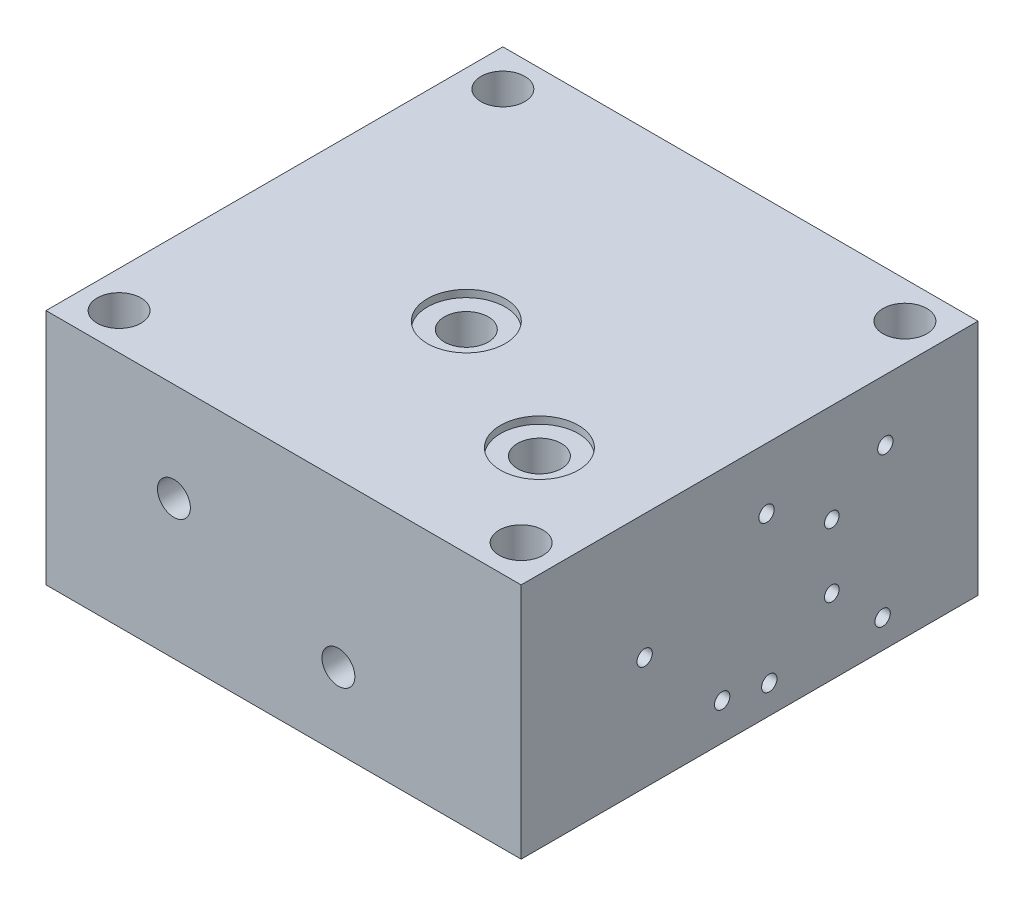
SolidWorks part; units mm, degrees
ref_plane "前视基准面" through (0, 0, 0) normal (0, 0, 1) x (1, 0, 0)
ref_plane "上视基准面" through (0, 0, 0) normal (0, 1, 0) x (1, 0, 0)
ref_plane "右视基准面" through (0, 0, 0) normal (1, 0, 0) x (0, 0, -1)
sketch "草图2" plane through (0, 0, 0) normal (0, 1, 0) x (1, 0, 0)
  line L1 (-65, -62.5) -> (65, -62.5)
  line L2 (-65, -62.5) -> (-65, 62.5)
  line L3 (-65, 62.5) -> (65, 62.5)
  line L4 (65, -62.5) -> (65, 62.5)
  line L5 (-65, -62.5) -> (65, 62.5) construction
  line L6 (-65, 62.5) -> (65, -62.5) construction
  circle A0 centre (-55, 52.5) radius 6
  circle A1 centre (55, 52.5) radius 6
  circle A2 centre (55, -52.5) radius 6
  circle A3 centre (-55, -52.5) radius 6
  point P0 (0, 0)
  dimension "D1" = 10
  dimension "D2" = 10
  dimension "D3" = 2
  dimension "D4" = 2
extrude "凸台-拉伸1" add sketch "草图2" along normal blind 65 contours A2 | A3 | A1 | L2 L3 L4 L1 | A0
sketch "草图19" plane through (-65, 0, 0) normal (-1, 0, 0) x (0, 0, 1)
  line L0 (-62.5, 65) -> (-62.5, 38)
  line L1 (-62.5, 65) -> (-62.5, 0) construction
  line L2 (-62.5, 38) -> (-22.5, 38)
hole_wizard "Ø4.0 (4) 直径孔5" positions "3D草图6" profile "草图20" hole size "Ø4.0" standard "GB" end condition through all
sketch3d "3D草图6"
  point P0 (-65, 38, -22.5)
sketch "草图20" plane through (-65, 38, -22.5) normal (0, 1, 0) x (0, 0, 1)
  line L0 (0, 0) -> (0, 130)
  line L1 (0, 130) -> (2, 130)
  line L2 (2, 130) -> (2, 0)
  line L5 (2, 0) -> (0, 0)
  line L11 (0, -6.35) -> (0, 107.95) construction
  dimension "通孔孔直径" = 4
  dimension "通孔孔深度" = 130
sketch "草图21" plane through (0, 0, -62.5) normal (0, 0, -1) x (-1, 0, 0)
  point P10 (-4.7, 9.8)
  point P11 (-12.2, 20.5)
  point P12 (-30.5, 9.8)
  point P13 (-23, 20.5)
  point P22 (-30.5, 31.2)
  point P23 (-4.7, 31.2)
  point P24 (-32.5, 20.5)
  point P25 (-17.6, 30.4)
  dimension "D3" = 27.8
  dimension "D4" = 12.9
  dimension "D5" = 10.7
  dimension "D6" = 20.6
  dimension "D7" = 21.4
  dimension "D8" = 25.8
  dimension "D1" = 7.5
  dimension "D2" = 18.3
sketch "草图26" plane through (65, 0, 0) normal (1, 0, 0) x (0, 0, -1)
  point P2 (-28.7046, 20.5)
  point P8 (5.4, 7.8)
  point P9 (4.65, 48.3)
  point P10 (37.15, 48.3)
  point P11 (36.4, 7.8)
  point P12 (22.4954, 38)
  point P13 (22.4954, 20.5)
  dimension "D1" = 40.5
  dimension "D2" = 0.75
  dimension "D3" = 31
  dimension "D4" = 31.75
  dimension "D5" = 30.2
  dimension "D6" = 12.7
hole_wizard "M5 螺纹孔3" positions "3D草图11" profile "草图27" tap size "M5" standard "GB"
sketch3d "3D草图11"
  point P0 (65, 48.3, -4.65)
  point P3 (65, 48.3, -37.15)
  point P6 (65, 7.8, -36.4)
  point P9 (65, 7.8, -5.4)
sketch "草图27" plane through (65, 48.3, -4.65) normal (0, 1, 0) x (0, 0, -1)
  line L0 (0, 0) -> (0, 13.2618)
  line L1 (0, 13.2618) -> (2.1, 12)
  line L2 (2.1, 12) -> (2.1, 0)
  line L5 (2.1, 0) -> (0, 0)
  line L10 (0, 13.2618) -> (-2.1, 12) construction
  line L11 (0, -6.35) -> (0, 107.95) construction
  dimension "螺纹孔钻头直径" = 4.2
  dimension "螺纹孔钻头深度" = 12
  dimension "导头角度" = 118
cosmetic thread "孔螺蚊线9" parameters "D1"=8, "D2"=5
cosmetic thread "孔螺蚊线10" parameters "D1"=8, "D2"=5
cosmetic thread "孔螺蚊线11" parameters "D1"=8, "D2"=5
cosmetic thread "孔螺蚊线12" parameters "D1"=8, "D2"=5
hole_wizard "Ø4.0 (4) 直径孔9" positions "3D草图12" profile "草图28" hole size "Ø4.0" standard "GB"
sketch3d "3D草图12"
  point P0 (65, 20.5, -22.4954)
sketch "草图28" plane through (65, 20.5, -22.4954) normal (0, 1, 0) x (0, 0, -1)
  line L0 (0, 0) -> (0, 33.7017)
  line L1 (0, 33.7017) -> (2, 32.5)
  line L2 (2, 32.5) -> (2, 0)
  line L5 (2, 0) -> (0, 0)
  line L10 (0, 33.7017) -> (-2, 32.5) construction
  line L11 (0, -6.35) -> (0, 107.95) construction
  dimension "孔直径" = 4
  dimension "孔深度" = 32.5
  dimension "导头角度" = 118
hole_wizard "Ø6.0 (6) 直径孔1" positions "3D草图13" profile "草图31" hole size "Ø6.0" standard "GB"
sketch3d "3D草图13"
  point P0 (32.5, 20.5, -62.5)
sketch "草图31" plane through (32.5, 20.5, -62.5) normal (1, 0, 0) x (0, 1, 0)
  line L0 (0, 0) -> (0, 43.8026)
  line L1 (0, 43.8026) -> (3, 42)
  line L2 (3, 42) -> (3, 0)
  line L5 (3, 0) -> (0, 0)
  line L10 (0, 43.8026) -> (-3, 42) construction
  line L11 (0, -6.35) -> (0, 107.95) construction
  dimension "孔直径" = 6
  dimension "孔深度" = 42
  dimension "导头角度" = 118
sketch "草图38" plane through (-65, 0, 0) normal (-1, 0, 0) x (0, 0, 1)
  point P0 (-22.5, 38)
  point P1 (-37, 52.5)
  point P6 (-8, 52.5)
  point P7 (-8, 23.5)
  point P8 (-37, 23.5)
  dimension "D1" = 14.5
  dimension "D2" = 14.5
  dimension "D3" = 2
  dimension "D4" = 2
hole_wizard "M6 螺纹孔1" positions "3D草图16" profile "草图39" tap size "M6" standard "GB"
sketch3d "3D草图16"
  point P0 (-65, 52.5, -37)
  point P3 (-65, 52.5, -8)
  point P6 (-65, 23.5, -37)
  point P9 (-65, 23.5, -8)
sketch "草图39" plane through (-65, 52.5, -37) normal (0, 1, 0) x (0, 0, 1)
  line L0 (0, 0) -> (0, 14.5022)
  line L1 (0, 14.5022) -> (2.5, 13)
  line L2 (2.5, 13) -> (2.5, 0)
  line L5 (2.5, 0) -> (0, 0)
  line L10 (0, 14.5022) -> (-2.5, 13) construction
  line L11 (0, -6.35) -> (0, 107.95) construction
  dimension "螺纹孔钻头直径" = 5
  dimension "螺纹孔钻头深度" = 13
  dimension "导头角度" = 118
cosmetic thread "孔螺蚊线13" parameters "D1"=8, "D2"=6
cosmetic thread "孔螺蚊线14" parameters "D1"=8, "D2"=6
cosmetic thread "孔螺蚊线15" parameters "D1"=8, "D2"=6
cosmetic thread "孔螺蚊线16" parameters "D1"=8, "D2"=6
sketch "草图40" plane through (0, 0, 62.5) normal (0, 0, 1) x (1, 0, 0)
  line L0 (-65, 38) -> (-30, 38)
hole_wizard "Ø4.0 (4) 直径孔11" positions "3D草图17" profile "草图41" hole size "Ø4.0" standard "GB"
sketch3d "3D草图17"
  point P0 (-30, 38, 62.5)
sketch "草图41" plane through (-30, 38, 62.5) normal (1, 0, 0) x (0, -1, 0)
  line L0 (0, 0) -> (0, 86.2017)
  line L1 (0, 86.2017) -> (2, 85)
  line L2 (2, 85) -> (2, 0)
  line L5 (2, 0) -> (0, 0)
  line L10 (0, 86.2017) -> (-2, 85) construction
  line L11 (0, -6.35) -> (0, 107.95) construction
  dimension "孔直径" = 4
  dimension "孔深度" = 85
  dimension "导头角度" = 118
hole_wizard "M10x1.0 螺纹孔1" positions "3D草图18" profile "草图42" tap size "M10x1.0" standard "GB"
sketch3d "3D草图18"
  point P0 (-30, 38, 62.5)
sketch "草图42" plane through (-30, 38, 62.5) normal (1, 0, 0) x (0, -1, 0)
  line L0 (0, 0) -> (0, 15.7039)
  line L1 (0, 15.7039) -> (4.5, 13)
  line L2 (4.5, 13) -> (4.5, 0)
  line L5 (4.5, 0) -> (0, 0)
  line L10 (0, 15.7039) -> (-4.5, 13) construction
  line L11 (0, -6.35) -> (0, 107.95) construction
  dimension "螺纹孔钻头直径" = 9
  dimension "螺纹孔钻头深度" = 13
  dimension "导头角度" = 118
cosmetic thread "孔螺蚊线17" parameters "D1"=8, "D2"=10
sketch "草图44" plane through (0, 0, 62.5) normal (0, 0, 1) x (1, 0, 0)
  line L0 (65, 0) -> (17.6, 0)
  line L1 (-65, 0) -> (65, 0) construction
  line L2 (17.6, 0) -> (17.6, 30.4)
sketch "草图46" plane through (0, 65, 0) normal (0, 1, 0) x (1, 0, 0)
  line L0 (65, -62.5) -> (35, -62.5)
  line L1 (65, -62.5) -> (17.6, -62.5) construction
  line L2 (35, -62.5) -> (35, -27.5)
  line L3 (65, 62.5) -> (-5, 62.5)
  line L4 (-65, 62.5) -> (65, 62.5) construction
  line L5 (-5, 62.5) -> (-5, -7.5)
hole_wizard "孔1" positions "3D草图22" profile "草图48" legacy
sketch3d "3D草图22"
  point P0 (-5, 65, 7.5)
  point P3 (35, 65, 27.5)
sketch "草图48" plane through (-5, 65, 7.5) normal (1, 0, 0) x (0, 0, 1)
  line L0 (0, 0) -> (0, 65)
  line L1 (0, 65) -> (6, 65)
  line L2 (6, 65) -> (6, 1.97)
  line L3 (6, 1.97) -> (10.65, 1.97)
  line L4 (10.65, 1.97) -> (10.65, 0)
  line L5 (10.65, 0) -> (0, 0)
  line L6 (0, 110) -> (0, -10) construction
  dimension "直径" = 12
  dimension "深度" = 65
  dimension "柱坑直径" = 21.3
  dimension "柱坑深度" = 1.97
sketch "草图50" plane through (0, 0, 0) normal (0, -1, 0) x (-1, 0, 0)
  line L0 (65, 62.5) -> (-23, 62.5)
  line L1 (65, 62.5) -> (-65, 62.5) construction
  line L2 (-23, 62.5) -> (-23, 3.7)
sketch "草图52" plane through (0, 0, -62.5) normal (0, 0, -1) x (-1, 0, 0)
  line L0 (-32.5, 20.5) -> (-23.7, 20.5)
  line L1 (-23.7, 20.5) -> (-23.7, 10.1)
  line L2 (-23.7, 20.5) -> (-23.7, 30.9)
  line L3 (-23.7, 20.5) -> (-15, 20.5)
  line L4 (-32.5, 20.5) -> (-32.5, 36)
  line L5 (-32.5, 36) -> (-45.2, 36)
  line L6 (-45.2, 36) -> (-4.7, 36)
  line L7 (-65, 36) -> (30, 36) construction
  line L8 (-4.7, 36) -> (-4.7, 5)
  line L9 (-45.2, 36) -> (-45.2, 5)
hole_wizard "M5 螺纹孔5" positions "3D草图25" profile "草图53" tap size "M5" standard "GB"
sketch3d "3D草图25"
  point P0 (4.7, 36, -62.5)
  point P3 (45.2, 36, -62.5)
  point P6 (45.2, 5, -62.5)
  point P9 (4.7, 5, -62.5)
sketch "草图53" plane through (4.7, 36, -62.5) normal (1, 0, 0) x (0, 1, 0)
  line L0 (0, 0) -> (0, 11.2618)
  line L1 (0, 11.2618) -> (2.1, 10)
  line L2 (2.1, 10) -> (2.1, 0)
  line L5 (2.1, 0) -> (0, 0)
  line L10 (0, 11.2618) -> (-2.1, 10) construction
  line L11 (0, -6.35) -> (0, 107.95) construction
  dimension "螺纹孔钻头直径" = 4.2
  dimension "螺纹孔钻头深度" = 10
  dimension "导头角度" = 118
cosmetic thread "孔螺蚊线25" parameters "D1"=8, "D2"=5
cosmetic thread "孔螺蚊线26" parameters "D1"=8, "D2"=5
cosmetic thread "孔螺蚊线27" parameters "D1"=8, "D2"=5
cosmetic thread "孔螺蚊线28" parameters "D1"=8, "D2"=5
hole_wizard "Ø6.0 (6) 直径孔2" positions "3D草图26" profile "草图54" hole size "Ø6.0" standard "GB"
sketch3d "3D草图26"
  point P0 (23.7, 10.1, -62.5)
sketch "草图54" plane through (23.7, 10.1, -62.5) normal (1, 0, 0) x (0, 1, 0)
  line L0 (0, 0) -> (0, 71.8026)
  line L1 (0, 71.8026) -> (3, 70)
  line L2 (3, 70) -> (3, 0)
  line L5 (3, 0) -> (0, 0)
  line L10 (0, 71.8026) -> (-3, 70) construction
  line L11 (0, -6.35) -> (0, 107.95) construction
  dimension "孔直径" = 6
  dimension "孔深度" = 70
  dimension "导头角度" = 118
hole_wizard "Ø6.0 (6) 直径孔3" positions "3D草图27" profile "草图55" hole size "Ø6.0" standard "GB"
sketch3d "3D草图27"
  point P0 (23.7, 30.9, -62.5)
sketch "草图55" plane through (23.7, 30.9, -62.5) normal (1, 0, 0) x (0, 1, 0)
  line L0 (0, 0) -> (0, 91.8026)
  line L1 (0, 91.8026) -> (3, 90)
  line L2 (3, 90) -> (3, 0)
  line L5 (3, 0) -> (0, 0)
  line L10 (0, 91.8026) -> (-3, 90) construction
  line L11 (0, -6.35) -> (0, 107.95) construction
  dimension "孔直径" = 6
  dimension "孔深度" = 90
  dimension "导头角度" = 118
sketch "草图56" plane through (65, 0, 0) normal (1, 0, 0) x (0, 0, -1)
  line L1 (62.5, 0) -> (-28.7046, 0)
  line L2 (-62.5, 0) -> (62.5, 0) construction
  line L3 (-28.7046, 0) -> (-28.7046, 30.9)
hole_wizard "M5 螺纹孔8" positions "3D草图30" profile "草图61" tap size "M5" standard "GB"
sketch3d "3D草图30"
  point P0 (65, 30.9, 28.7046)
sketch "草图61" plane through (65, 30.9, 28.7046) normal (0, 1, 0) x (0, 0, -1)
  line L0 (0, 0) -> (0, 42.5718)
  line L1 (0, 42.5718) -> (2.1, 41.31)
  line L2 (2.1, 41.31) -> (2.1, 0)
  line L5 (2.1, 0) -> (0, 0)
  line L10 (0, 42.5718) -> (-2.1, 41.31) construction
  line L11 (0, -6.35) -> (0, 107.95) construction
  dimension "螺纹孔钻头直径" = 4.2
  dimension "螺纹孔钻头深度" = 41.31
  dimension "导头角度" = 118
cosmetic thread "孔螺蚊线31" parameters "D1"=10, "D2"=5
hole_wizard "Ø6.0 (6) 直径孔4" positions "3D草图31" profile "草图62" hole size "Ø6.0" standard "GB" end condition through all
sketch3d "3D草图31"
  point P0 (15, 20.5, -62.5)
sketch "草图62" plane through (15, 20.5, -62.5) normal (1, 0, 0) x (0, 1, 0)
  line L0 (0, 0) -> (0, 125)
  line L1 (0, 125) -> (3, 125)
  line L2 (3, 125) -> (3, 0)
  line L5 (3, 0) -> (0, 0)
  line L11 (0, -6.35) -> (0, 107.95) construction
  dimension "通孔孔直径" = 6
  dimension "通孔孔深度" = 125
sketch "草图65" plane through (0, 0, 62.5) normal (0, 0, 1) x (1, 0, 0)
  line L0 (65, 0) -> (15, 0)
  line L1 (-65, 0) -> (65, 0) construction
  line L2 (15, 0) -> (15, 20.5)
hole_wizard "M10x1.0 螺纹孔2" positions "3D草图32" profile "草图66" tap size "M10x1.0" standard "GB"
sketch3d "3D草图32"
  point P0 (15, 20.5, 62.5)
sketch "草图66" plane through (15, 20.5, 62.5) normal (1, 0, 0) x (0, -1, 0)
  line L0 (0, 0) -> (0, 15.7039)
  line L1 (0, 15.7039) -> (4.5, 13)
  line L2 (4.5, 13) -> (4.5, 0)
  line L5 (4.5, 0) -> (0, 0)
  line L10 (0, 15.7039) -> (-4.5, 13) construction
  line L11 (0, -6.35) -> (0, 107.95) construction
  dimension "螺纹孔钻头直径" = 9
  dimension "螺纹孔钻头深度" = 13
  dimension "导头角度" = 118
cosmetic thread "孔螺蚊线32" parameters "D1"=8, "D2"=10
sketch "草图70" plane through (65, 0, 0) normal (1, 0, 0) x (0, 0, -1)
  line L0 (62.5, 9.8) -> (-7.5, 10.1)
  line L1 (-7.5, 13.1) -> (-7.5, 7.1) construction
hole_wizard "M5 螺纹孔9" positions "3D草图35" profile "草图71" tap size "M5" standard "GB"
sketch3d "3D草图35"
  point P0 (65, 10.1, 7.5)
sketch "草图71" plane through (65, 10.1, 7.5) normal (0, 1, 0) x (0, 0, -1)
  line L0 (0, 0) -> (0, 71.2618)
  line L1 (0, 71.2618) -> (2.1, 70)
  line L2 (2.1, 70) -> (2.1, 0)
  line L5 (2.1, 0) -> (0, 0)
  line L10 (0, 71.2618) -> (-2.1, 70) construction
  line L11 (0, -6.35) -> (0, 107.95) construction
  dimension "螺纹孔钻头直径" = 4.2
  dimension "螺纹孔钻头深度" = 70
  dimension "导头角度" = 118
cosmetic thread "孔螺蚊线33" parameters "D1"=10, "D2"=5
